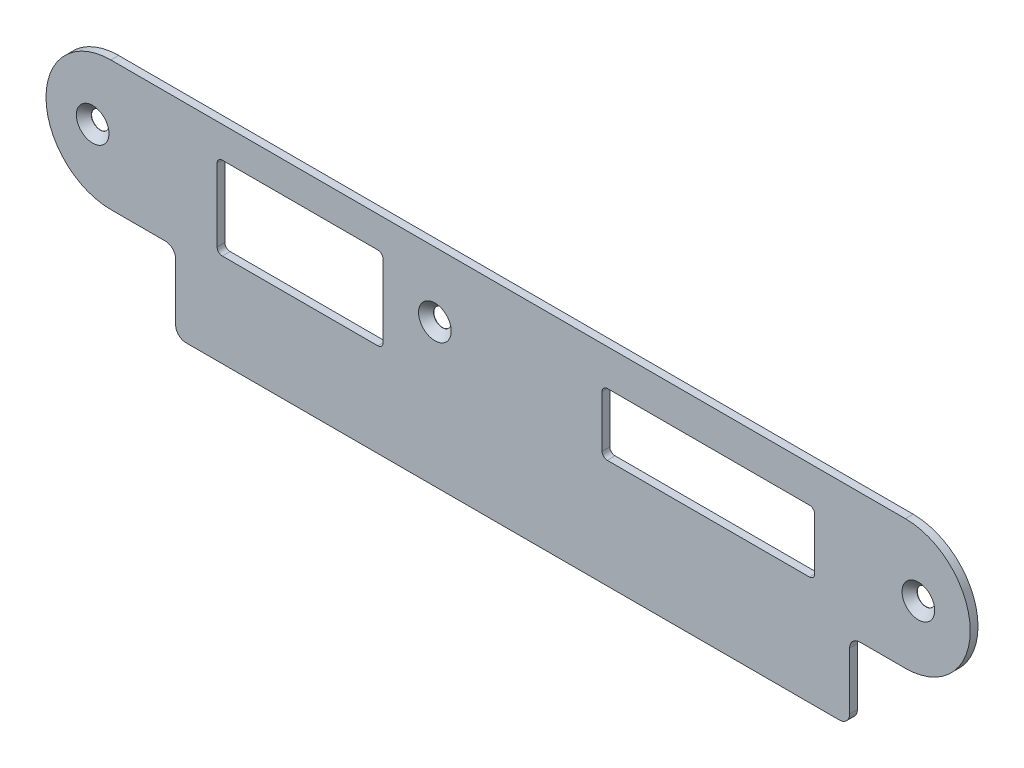
SolidWorks part; units mm, degrees
ref_plane "Plan de face" through (0, 0, 0) normal (0, 0, 1) x (1, 0, 0)
ref_plane "Plan de dessus" through (0, 0, 0) normal (0, 1, 0) x (1, 0, 0)
ref_plane "Plan de droite" through (0, 0, 0) normal (1, 0, 0) x (0, 0, -1)
sketch "Esquisse1" plane through (0, 0, 0) normal (0, 0, 1) x (1, 0, 0)
  line L0 (-31.5, 13) -> (-61.5, 13) construction
  line L1 (-30.5, -2) -> (-30.5, 12) construction
  line L2 (-61.5, -3) -> (-31.5, -3) construction
  line L3 (-62.5, 12) -> (-62.5, -2) construction
  line L4 (-31.5, 13) -> (-61.5, 13)
  line L5 (-30.5, -2) -> (-30.5, 12)
  line L6 (-83, -6) -> (-72.5, -6)
  line L7 (-70.5, -8) -> (-70.5, -19)
  line L8 (-68.5, -21) -> (57.5, -21)
  line L9 (59.5, -19) -> (59.5, -8)
  line L10 (61.5, -6) -> (70.25, -6)
  line L11 (70.25, 19) -> (-83, 19)
  line L12 (-83, -6) -> (-72.5, -6)
  line L13 (-70.5, -8) -> (-70.5, -19)
  line L14 (-68.5, -21) -> (57.5, -21)
  line L15 (59.5, -19) -> (59.5, -8)
  line L16 (61.5, -6) -> (70.25, -6)
  line L17 (70.25, 19) -> (-83, 19)
  line L18 (-61.5, -3) -> (-31.5, -3)
  line L19 (-62.5, 12) -> (-62.5, -2)
  line L20 (51.75, 12) -> (12.75, 12) construction
  line L21 (11.75, 11) -> (11.75, 1) construction
  line L22 (12.75, 0) -> (51.75, 0) construction
  line L23 (52.75, 1) -> (52.75, 11) construction
  line L24 (51.75, 12) -> (12.75, 12)
  line L25 (11.75, 11) -> (11.75, 1)
  line L26 (12.75, 0) -> (51.75, 0)
  line L27 (52.75, 1) -> (52.75, 11)
  circle A1 centre (-86.5, 6.5) radius 1
  arc A2 (-61.5, 13) -> (-62.5, 12) centre (-61.5, 12) ccw construction
  arc A3 (-30.5, 12) -> (-31.5, 13) centre (-31.5, 12) ccw construction
  arc A4 (-31.5, -3) -> (-30.5, -2) centre (-31.5, -2) ccw construction
  arc A5 (-62.5, -2) -> (-61.5, -3) centre (-61.5, -2) ccw construction
  arc A6 (-83, 19) -> (-83, -6) centre (-83, 6.5) ccw
  arc A7 (-70.5, -8) -> (-72.5, -6) centre (-72.5, -8) ccw
  arc A8 (-70.5, -19) -> (-68.5, -21) centre (-68.5, -19) ccw
  arc A9 (57.5, -21) -> (59.5, -19) centre (57.5, -19) ccw
  arc A10 (61.5, -6) -> (59.5, -8) centre (61.5, -8) ccw
  arc A11 (70.25, -6) -> (70.25, 19) centre (70.25, 6.5) ccw
  arc A12 (-83, 19) -> (-83, -6) centre (-83, 6.5) ccw
  arc A13 (-70.5, -8) -> (-72.5, -6) centre (-72.5, -8) ccw
  arc A14 (-70.5, -19) -> (-68.5, -21) centre (-68.5, -19) ccw
  arc A15 (57.5, -21) -> (59.5, -19) centre (57.5, -19) ccw
  arc A16 (61.5, -6) -> (59.5, -8) centre (61.5, -8) ccw
  arc A17 (70.25, -6) -> (70.25, 19) centre (70.25, 6.5) ccw
  arc A18 (-61.5, 13) -> (-62.5, 12) centre (-61.5, 12) ccw
  arc A19 (-30.5, 12) -> (-31.5, 13) centre (-31.5, 12) ccw
  arc A20 (-31.5, -3) -> (-30.5, -2) centre (-31.5, -2) ccw
  arc A21 (-62.5, -2) -> (-61.5, -3) centre (-61.5, -2) ccw
  circle A23 centre (-20.5, 6.5) radius 1
  arc A24 (52.75, 11) -> (51.75, 12) centre (51.75, 11) ccw construction
  arc A25 (12.75, 12) -> (11.75, 11) centre (12.75, 11) ccw construction
  arc A26 (11.75, 1) -> (12.75, 0) centre (12.75, 1) ccw construction
  arc A27 (51.75, 0) -> (52.75, 1) centre (51.75, 1) ccw construction
  arc A28 (52.75, 11) -> (51.75, 12) centre (51.75, 11) ccw
  arc A29 (12.75, 12) -> (11.75, 11) centre (12.75, 11) ccw
  arc A30 (11.75, 1) -> (12.75, 0) centre (12.75, 1) ccw
  arc A31 (51.75, 0) -> (52.75, 1) centre (51.75, 1) ccw
  circle A33 centre (72.75, 6.5) radius 1
  dimension "D2" = 2
  dimension "D3" = 2
  dimension "D4" = 2
  dimension "D1" = 0
extrude "Extrusion1" add sketch "Esquisse1" along normal blind 1.5
hole_wizard "Fraisage pour vis à tête fraisée M31" positions "Esquisse3D1" profile "Esquisse2" countersink size "M3" standard "ISO" end condition through all
sketch3d "Esquisse3D1"
  line L4 (72.75, 6.5, 1.5) -> (72.75, 6.5, 0) construction
  line L5 (-20.5, 6.5, 1.5) -> (-20.5, 6.5, 0) construction
  line L6 (-86.5, 6.5, 1.5) -> (-86.5, 6.5, 0) construction
  point P28 (-86.5, 6.5, 1.5)
  point P35 (-20.5, 6.5, 1.5)
  point P37 (72.75, 6.5, 1.5)
sketch "Esquisse2" plane through (-86.5, 6.5, 1.5) normal (1, 0, 0) x (0, -1, 0)
  line L0 (0, 0) -> (0, 1.5)
  line L1 (0, 1.5) -> (1.7, 1.5)
  line L2 (1.7, 1.5) -> (1.7, 1.45)
  line L3 (1.7, 1.45) -> (3.15, 0)
  line L5 (3.15, 0) -> (0, 0)
  line L6 (-1.7, 1.45) -> (-3.15, 0) construction
  line L11 (0, -6.35) -> (0, 107.95) construction
  dimension "Diamètre du perçage jusqu'au prochain" = 3.4
  dimension "Profondeur du perçage jusqu'au prochain" = 1.5
  dimension "Diamètre du fraisage entrant" = 6.3
  dimension "Angle du fraisage entrant" = 90
